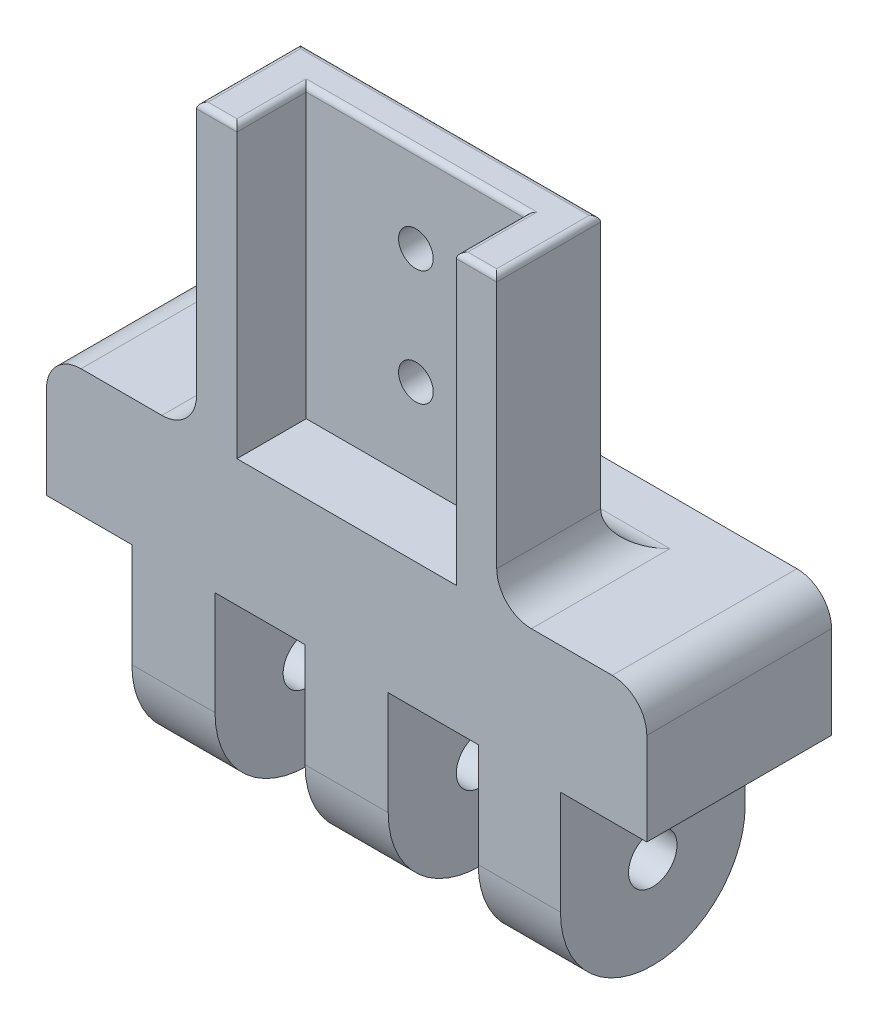
SolidWorks part; units mm, degrees
ref_plane "Front Plane" through (0, 0, 0) normal (0, 0, 1) x (1, 0, 0)
ref_plane "Top Plane" through (0, 0, 0) normal (0, 1, 0) x (1, 0, 0)
ref_plane "Right Plane" through (0, 0, 0) normal (1, 0, 0) x (0, 0, -1)
sketch "Sketch2" plane through (0, 0, 0) normal (1, 0, 0) x (0, 0, -1)
  line L2 (-8, 0) -> (-8, 20)
  line L3 (-8, 20) -> (8, 20)
  line L4 (8, 0) -> (8, 20)
  circle A0 centre (0, 0) radius 2.1
  arc A1 (-8, 0) -> (8, 0) centre (0, 0) ccw
  dimension "D1" = 16
  dimension "D2" = 4.2
  dimension "D3" = 20
extrude "Boss-Extrude1" add sketch "Sketch2" along normal mid plane 52
sketch "Sketch3" plane through (0, 0, 8) normal (0, 0, 1) x (1, 0, 0)
  line L0 (26, 0) -> (-26, 0) construction
  line L1 (-26, -9) -> (-18.6, -9)
  line L2 (-26, -9) -> (-26, 9)
  line L3 (-26, 9) -> (-18.6, 9)
  line L4 (-18.6, -9) -> (-18.6, 9)
  line L5 (-26, -9) -> (-18.6, 9) construction
  line L6 (-26, 9) -> (-18.6, -9) construction
  line L8 (-11.4, -9) -> (-3.6, -9)
  line L9 (-11.4, -9) -> (-11.4, 9)
  line L10 (-11.4, 9) -> (-3.6, 9)
  line L11 (-3.6, -9) -> (-3.6, 9)
  line L12 (-11.4, -9) -> (-3.6, 9) construction
  line L13 (-11.4, 9) -> (-3.6, -9) construction
  line L14 (3.6, -9) -> (11.4, -9)
  line L15 (3.6, -9) -> (3.6, 9)
  line L16 (3.6, 9) -> (11.4, 9)
  line L17 (11.4, -9) -> (11.4, 9)
  line L18 (3.6, -9) -> (11.4, 9) construction
  line L19 (3.6, 9) -> (11.4, -9) construction
  line L20 (-26, 20) -> (-26, 0) construction
  line L21 (26, 20) -> (26, 0) construction
  line L22 (18.519, -9) -> (26, -9)
  line L23 (18.519, -9) -> (18.519, 9)
  line L24 (18.519, 9) -> (26, 9)
  line L25 (26, -9) -> (26, 9)
  line L26 (18.519, -9) -> (26, 9) construction
  line L27 (18.519, 9) -> (26, -9) construction
  point P0 (-22.3, 0)
  point P7 (-7.5, 0)
  point P12 (7.5, 0)
  point P17 (-22.3, 9)
  point P20 (22.2595, 0)
  dimension "D1" = 9
  dimension "D4" = 7.2
  dimension "D6" = 7.2
  dimension "D2" = 7.8
  dimension "D3" = 14.6
extrude "Cut-Extrude1" cut sketch "Sketch3" against normal through all
ref_plane "Plane1" through (0, 20, 0) normal (0, 1, 0) x (1, 0, 0)
sketch "Sketch4" plane through (0, 20, 0) normal (0, 1, 0) x (1, 0, 0)
  line L0 (26, 8) -> (26, -8) construction
  line L1 (13, -8) -> (-13, -8)
  line L2 (13, -8) -> (13, 1)
  line L3 (13, 1) -> (-13, 1)
  line L4 (-13, -8) -> (-13, 1)
  line L5 (13, -8) -> (-13, 1) construction
  line L6 (13, 1) -> (-13, -8) construction
  line L8 (26, -8) -> (-26, -8) construction
  point P0 (0, -3.5)
  dimension "D1" = 26
  dimension "D2" = 9
  dimension "D3" = 26
extrude "Boss-Extrude2" add sketch "Sketch4" along normal blind 25
ref_plane "Plane2" through (0, 45, 0) normal (0, 1, 0) x (1, 0, 0)
sketch "Sketch5" plane through (0, 45, 0) normal (0, 1, 0) x (1, 0, 0)
  line L0 (13, -8) -> (13, 1) construction
  line L1 (-9.5, -2) -> (9.5, -2)
  line L2 (-9.5, -2) -> (-9.5, -8)
  line L3 (-9.5, -8) -> (9.5, -8)
  line L4 (9.5, -2) -> (9.5, -8)
  line L5 (-9.5, -2) -> (9.5, -8) construction
  line L6 (-9.5, -8) -> (9.5, -2) construction
  line L7 (-13, -8) -> (13, -8) construction
  point P0 (0, -5)
  dimension "D1" = 19
  dimension "D2" = 13
  dimension "D3" = 6
extrude "Cut-Extrude2" cut sketch "Sketch5" against normal blind 25
fillet "Fillet1" radius 3 3 edges at (13, 20, 3.5) (0, 20, -1) (-13, 20, 3.5)
fillet "Fillet2" radius 3 2 edges at (26, 20, 0) (-26, 20, 0)
fillet "Fillet3" radius 0.5 8 edges at (13, 45, 3.5) (9.5, 45, 5) (11.25, 45, 8) (-11.25, 45, 8) (-9.5, 45, 5) (0, 45, 2) (0, 45, -1) (-13, 45, 3.5)
sketch "Sketch6" plane through (0, 0, 0) normal (0, 0, 1) x (1, 0, 0)
  line L0 (9.5, 20) -> (9.5, 44.5) construction
  line L1 (-16.3932, 32.5) -> (15.2785, 32.5) construction
  line L2 (9.5, 20) -> (-9.5, 20) construction
  circle A0 centre (0, 37.5) radius 1.5
  circle A1 centre (0, 27.5) radius 1.5
  dimension "D1" = 3
  dimension "D2" = 9.5
  dimension "D3" = 10
  dimension "D4" = 5
  dimension "D5" = 12.5
extrude "Cut-Extrude3" cut sketch "Sketch6" against normal mid plane 25
equation "\"hingewidth\"=7.2"
equation "\"fingerwidth\"=10.5"
equation "\"gapwidth\"=7.4"
equation "\"D4@Sketch3\"=\"hingewidth\""
equation "\"D6@Sketch3\"=\"hingewidth\""
